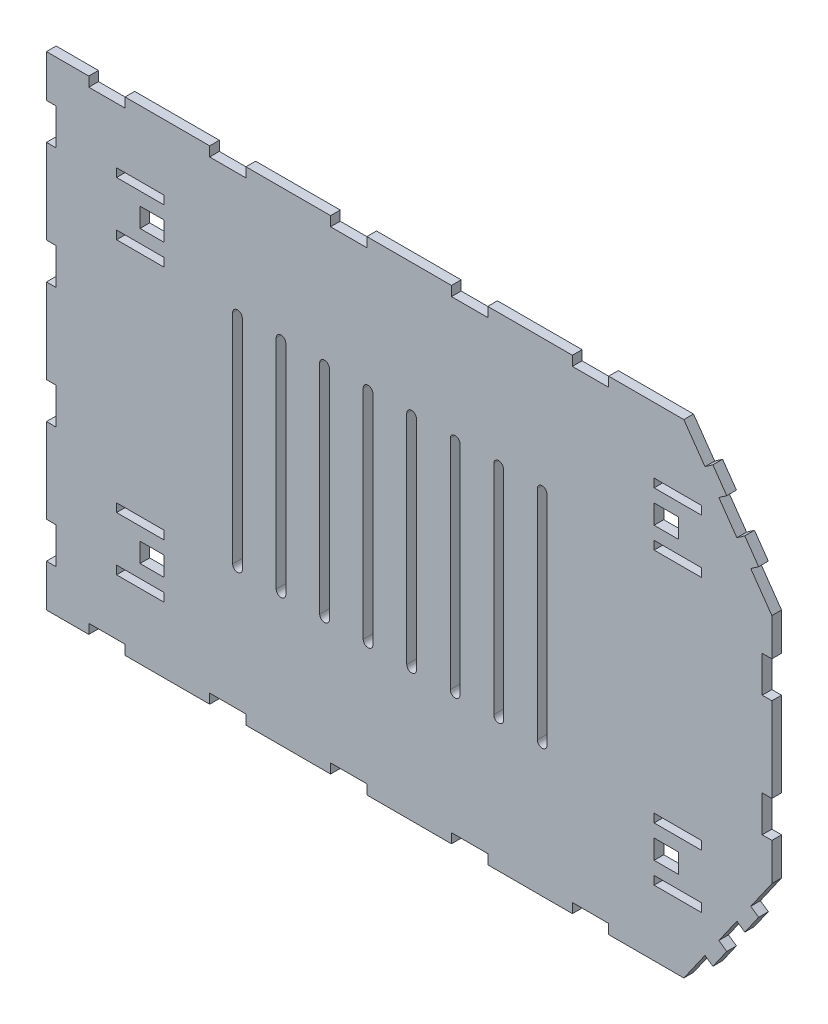
SolidWorks part; units mm, degrees
ref_plane "Ebene vorne" through (0, 0, 0) normal (0, 0, 1) x (1, 0, 0)
ref_plane "Ebene oben" through (0, 0, 0) normal (0, 1, 0) x (1, 0, 0)
ref_plane "Ebene rechts" through (0, 0, 0) normal (1, 0, 0) x (0, 0, -1)
sketch "Skizze2" plane through (0, 0, 0) normal (0, 0, 1) x (1, 0, 0)
  line L0 (0, 0) -> (0, 200)
  line L2 (300, 200) -> (300, 0)
  line L3 (300, 0) -> (0, 0)
  line L27 (0, 200) -> (300, 200)
  line L28 (-19.2774, 100) -> (328.8918, 100) construction
  line L29 (150, 271.2525) -> (150, -18.7771) construction
  dimension "D2" = 300
extrude "Aufsatz-Linear austragen1" add sketch "Skizze2" along normal blind 4 contours L0 L27 L2 L3
sketch "Skizze3" plane through (0, 0, 4) normal (0, 0, 1) x (1, 0, 0)
  line L0 (0, 200) -> (300, 200) construction
  line L1 (17.5, 200) -> (32.5, 200)
  line L2 (17.5, 200) -> (17.5, 196)
  line L3 (17.5, 196) -> (32.5, 196)
  line L4 (32.5, 200) -> (32.5, 196)
  line L5 (0, 0) -> (0, 200) construction
  dimension "D1" = 17.5
  dimension "D2" = 15
  dimension "D3" = 4
extrude "Schnitt-Linear austragen1" cut sketch "Skizze3" against normal up to next (4 mm away)
pattern_linear "Lineares Muster1" count 6 spacing 50 along (1, 0, 0) of "Schnitt-Linear austragen1"
ref_plane "Ebene1" through (0, 100, 0) normal (0, 1, 0) x (1, 0, 0)
mirror "Spiegeln1" about plane through (0, 100, 0) normal (0, 1, 0) of "Lineares Muster1", "Schnitt-Linear austragen1"
sketch "Skizze4" plane through (0, 0, 4) normal (0, 0, 1) x (1, 0, 0)
  line L1 (0, 0) -> (0, 200) construction
  line L2 (0, 182.5) -> (4, 182.5)
  line L3 (0, 182.5) -> (0, 167.5)
  line L4 (0, 167.5) -> (4, 167.5)
  line L5 (4, 182.5) -> (4, 167.5)
  line L6 (0, 200) -> (17.5, 200) construction
  dimension "D1" = 17.5
  dimension "D2" = 15
  dimension "D3" = 4
extrude "Schnitt-Linear austragen2" cut sketch "Skizze4" against normal up to next (4 mm away)
pattern_linear "Lineares Muster2" count 4 spacing 50 along (0, -1, 0) of "Schnitt-Linear austragen2"
ref_plane "Ebene2" through (150, 0, 0) normal (-1, 0, 0) x (0, 0, 1)
mirror "Spiegeln2" about plane through (150, 0, 0) normal (-1, 0, 0) of "Lineares Muster2", "Schnitt-Linear austragen2"
sketch "Skizze5" plane through (0, 0, 4) normal (0, 0, 1) x (1, 0, 0)
  line L1 (29, 172.9) -> (48.7, 172.9)
  line L2 (29, 172.9) -> (29, 169.4)
  line L3 (29, 169.4) -> (48.7, 169.4)
  line L4 (48.7, 172.9) -> (48.7, 169.4)
  line L5 (29, 150.6) -> (48.7, 150.6)
  line L6 (29, 150.6) -> (29, 147.1)
  line L7 (29, 147.1) -> (48.7, 147.1)
  line L8 (48.7, 150.6) -> (48.7, 147.1)
  line L9 (4, 167.5) -> (4, 182.5) construction
  line L12 (8.7951, 160) -> (77.9949, 160) construction
  line L13 (2.2, 100) -> (-2.2, 100) construction
  dimension "D1" = 3.5
  dimension "D2" = 18.8
  dimension "D3" = 60
  dimension "D4" = 25
  dimension "D5" = 19.7
extrude "Schnitt-Linear austragen3" cut sketch "Skizze5" against normal up to next (4 mm away)
mirror "Spiegeln3" about plane through (150, 0, 0) normal (-1, 0, 0) of "Schnitt-Linear austragen3"
mirror "Spiegeln4" about plane through (0, 100, 0) normal (0, 1, 0) of "Spiegeln3", "Schnitt-Linear austragen3"
sketch "Skizze7" plane through (0, 0, 4) normal (0, 0, 1) x (1, 0, 0)
  line L1 (267.5, 0) -> (232.5, 0) construction
  line L2 (300, 67.5) -> (300, 32.5) construction
  line L8 (263.5892, 0) -> (272.3306, 12.484)
  line L10 (278.0664, 20.6755) -> (281.343, 18.3812)
  line L11 (281.343, 18.3812) -> (275.6072, 10.1897)
  line L12 (275.6072, 10.1897) -> (272.3306, 12.484)
  line L14 (285.5229, 31.3245) -> (288.7995, 29.0302)
  line L15 (288.7995, 29.0302) -> (294.5352, 37.2217)
  line L16 (294.5352, 37.2217) -> (291.2586, 39.516)
  line L17 (291.2586, 39.516) -> (300, 52)
  line L18 (263.5892, 0) -> (300, 0)
  line L24 (300, 0) -> (300, 52)
  line L25 (264.7225, 37.954) -> (321.2021, -1.5934) construction
  line L26 (278.0664, 20.6755) -> (285.5229, 31.3245)
  line L27 (276.6176, 43.6639) -> (330.1871, 6.1541) construction
  dimension "D1" = 52
  dimension "D2" = 4
  dimension "D3" = 11.5
  dimension "D4" = 10
  dimension "D5" = 55
extrude "Schnitt-Linear austragen4" cut sketch "Skizze7" against normal up to next (4 mm away)
mirror "Spiegeln5" about plane through (0, 100, 0) normal (0, 1, 0) of "Schnitt-Linear austragen4"
sketch "Skizze8" plane through (0, 0, 4) normal (0, 0, 1) x (1, 0, 0)
  line L0 (214.5174, 160) -> (319.1831, 160) construction
  line L1 (251.3, 164) -> (261.3, 164)
  line L2 (251.3, 164) -> (251.3, 156)
  line L3 (251.3, 156) -> (261.3, 156)
  line L4 (261.3, 164) -> (261.3, 156)
  line L5 (271, 169.4) -> (251.3, 169.4) construction
  line L6 (251.3, 150.6) -> (271, 150.6) construction
  line L7 (256.3, 185.256) -> (256.3, 129.907) construction
  line L8 (251.3, 169.4) -> (251.3, 172.9) construction
  dimension "D1" = 10
  dimension "D2" = 8
extrude "Schnitt-Linear austragen5" cut sketch "Skizze8" against normal up to next (4 mm away)
mirror "Spiegeln6" about plane through (150, 0, 0) normal (-1, 0, 0) of "Schnitt-Linear austragen5"
mirror "Spiegeln7" about plane through (0, 100, 0) normal (0, 1, 0) of "Spiegeln6", "Schnitt-Linear austragen5"
sketch "Skizze9" plane through (0, 0, 4) normal (0, 0, 1) x (1, 0, 0)
  line L0 (2.2, 100) -> (-2.2, 100) construction
  line L1 (207, 100) -> (203, 100)
  line L2 (207, 100) -> (207, 145)
  line L4 (203, 100) -> (203, 145)
  line L5 (150, 2.2) -> (150, -2.2) construction
  arc A0 (203, 145) -> (207, 145) centre (205, 145) cw
  point P7 (0, 0)
  dimension "D1" = 4
  dimension "D2" = 45
  dimension "D3" = 55
extrude "Schnitt-Linear austragen6" cut sketch "Skizze9" against normal up to next (4 mm away)
mirror "Spiegeln8" about plane through (0, 100, 0) normal (0, 1, 0) of "Schnitt-Linear austragen6"
pattern_linear "Lineares Muster3" count 8 spacing 18 along (-1, 0, 0) of "Spiegeln8", "Schnitt-Linear austragen6"
